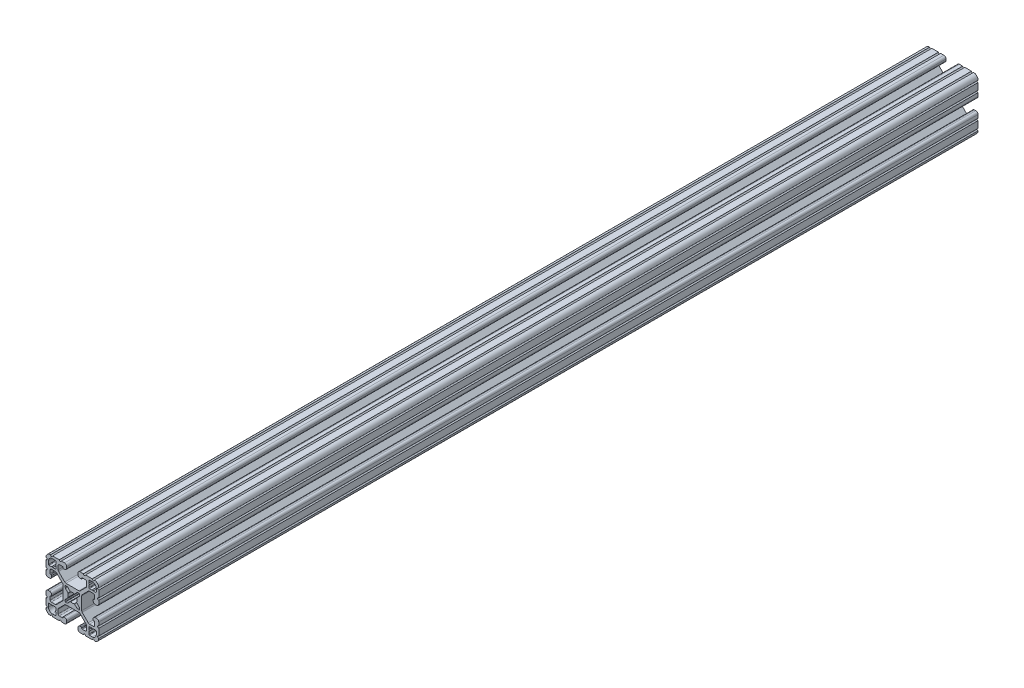
SolidWorks part; units mm, degrees
ref_plane "Front Plane" through (0, 0, 0) normal (0, 0, 1) x (1, 0, 0)
ref_plane "Top Plane" through (0, 0, 0) normal (0, 1, 0) x (1, 0, 0)
ref_plane "Right Plane" through (0, 0, 0) normal (1, 0, 0) x (0, 0, -1)
sketch "Sketch1" plane through (0, 0, 0) normal (0, 0, 1) x (1, 0, 0)
  line L0 (1.5823, 3.1988) -> (3.2921, 4.9085)
  line L1 (3.9207, 5.1689) -> (4.9149, 5.1689)
  line L2 (5.1689, 4.9149) -> (5.1689, 3.9207)
  line L3 (4.9085, 3.2921) -> (3.1988, 1.5823)
  line L4 (3.1988, -1.5823) -> (4.9085, -3.2921)
  line L5 (5.1689, -3.9207) -> (5.1689, -4.9149)
  line L6 (4.9149, -5.1689) -> (3.9207, -5.1689)
  line L7 (3.2921, -4.9085) -> (1.5823, -3.1988)
  line L8 (-1.5823, -3.1988) -> (-3.2921, -4.9085)
  line L9 (-3.9207, -5.1689) -> (-4.9149, -5.1689)
  line L10 (-5.1689, -4.9149) -> (-5.1689, -3.9207)
  line L11 (-4.9085, -3.2921) -> (-3.1988, -1.5823)
  line L12 (-3.1988, 1.5823) -> (-4.9085, 3.2921)
  line L13 (-5.1689, 3.9207) -> (-5.1689, 4.9149)
  line L14 (-4.9149, 5.1689) -> (-3.9207, 5.1689)
  line L15 (-3.2921, 4.9085) -> (-1.5823, 3.1988)
  line L16 (-11.8669, 14.0194) -> (-11.8669, 12.2479)
  line L17 (-12.2479, 11.8669) -> (-14.0195, 11.8669)
  line L18 (-14.0213, 11.8676) -> (-14.5575, 12.4039)
  line L19 (-14.5611, 12.4039) -> (-15.0973, 11.8676)
  line L20 (-15.0991, 11.8669) -> (-16.8707, 11.8669)
  line L21 (-17.2517, 12.2479) -> (-17.2517, 14.4577)
  line L22 (-14.4577, 17.2517) -> (-12.2479, 17.2517)
  line L23 (-11.8669, 16.8707) -> (-11.8669, 15.0991)
  line L24 (-11.8676, 15.0973) -> (-12.4039, 14.5611)
  line L25 (-12.4039, 14.5575) -> (-11.8676, 14.0212)
  line L26 (-14.0194, -11.8669) -> (-12.2479, -11.8669)
  line L27 (-11.8669, -12.2479) -> (-11.8669, -14.0195)
  line L28 (-11.8676, -14.0213) -> (-12.4039, -14.5575)
  line L29 (-12.4039, -14.5611) -> (-11.8676, -15.0973)
  line L30 (-11.8669, -15.0991) -> (-11.8669, -16.8707)
  line L31 (-12.2479, -17.2517) -> (-14.4577, -17.2517)
  line L32 (-17.2517, -14.4577) -> (-17.2517, -12.2479)
  line L33 (-16.8707, -11.8669) -> (-15.0991, -11.8669)
  line L34 (-15.0973, -11.8676) -> (-14.5611, -12.4039)
  line L35 (-14.5575, -12.4039) -> (-14.0212, -11.8676)
  line L36 (11.8669, -14.0194) -> (11.8669, -12.2479)
  line L37 (12.2479, -11.8669) -> (14.0195, -11.8669)
  line L38 (14.0213, -11.8676) -> (14.5575, -12.4039)
  line L39 (14.5611, -12.4039) -> (15.0973, -11.8676)
  line L40 (15.0991, -11.8669) -> (16.8707, -11.8669)
  line L41 (17.2517, -12.2479) -> (17.2517, -14.4577)
  line L42 (14.4577, -17.2517) -> (12.2479, -17.2517)
  line L43 (11.8669, -16.8707) -> (11.8669, -15.0991)
  line L44 (11.8676, -15.0973) -> (12.4039, -14.5611)
  line L45 (12.4039, -14.5575) -> (11.8676, -14.0212)
  line L46 (14.0194, 11.8669) -> (12.2479, 11.8669)
  line L47 (11.8669, 12.2479) -> (11.8669, 14.0195)
  line L48 (11.8676, 14.0213) -> (12.4039, 14.5575)
  line L49 (12.4039, 14.5611) -> (11.8676, 15.0973)
  line L50 (11.8669, 15.0991) -> (11.8669, 16.8707)
  line L51 (12.2479, 17.2517) -> (14.4577, 17.2517)
  line L52 (17.2517, 14.4577) -> (17.2517, 12.2479)
  line L53 (16.8707, 11.8669) -> (15.0991, 11.8669)
  line L54 (15.0973, 11.8676) -> (14.5611, 12.4039)
  line L55 (14.5575, 12.4039) -> (14.0212, 11.8676)
  line L56 (6.3498, -14.9848) -> (5.6531, -14.9848)
  line L57 (4.0778, -16.5601) -> (4.0778, -17.4747)
  line L58 (5.6531, -19.05) -> (7.9756, -19.05)
  line L59 (9.4996, -19.05) -> (14.2981, -19.05)
  line L60 (19.05, -14.3256) -> (19.05, -9.4996)
  line L61 (19.05, -7.9756) -> (19.05, -5.6531)
  line L62 (17.4747, -4.0778) -> (16.5601, -4.0778)
  line L63 (14.9848, -5.6531) -> (14.9848, -6.3498)
  line L64 (15.3661, -6.731) -> (15.6969, -6.731)
  line L65 (16.0782, -7.1122) -> (16.0782, -9.3968)
  line L66 (15.1881, -10.287) -> (12.3526, -10.2871)
  line L67 (11.4535, -9.9142) -> (7.1147, -5.5659)
  line L68 (6.7437, -4.6689) -> (6.7437, 4.6414)
  line L69 (7.1147, 5.5384) -> (11.481, 9.9142)
  line L70 (12.38, 10.2871) -> (15.1881, 10.287)
  line L71 (16.0782, 9.3968) -> (16.0782, 7.1122)
  line L72 (15.6969, 6.731) -> (15.3661, 6.731)
  line L73 (14.9848, 6.3498) -> (14.9848, 5.6531)
  line L74 (16.5601, 4.0778) -> (17.4747, 4.0778)
  line L75 (19.05, 5.6531) -> (19.05, 7.9756)
  line L76 (19.05, 9.4996) -> (19.05, 14.2981)
  line L77 (14.3256, 19.05) -> (9.4996, 19.05)
  line L78 (7.9756, 19.05) -> (5.6531, 19.05)
  line L79 (4.0778, 17.4747) -> (4.0778, 16.5601)
  line L80 (5.6531, 14.9848) -> (6.3498, 14.9848)
  line L81 (6.731, 15.3661) -> (6.731, 15.6969)
  line L82 (7.1122, 16.0782) -> (9.3968, 16.0782)
  line L83 (10.287, 15.1881) -> (10.2871, 12.3526)
  line L84 (9.9142, 11.4535) -> (5.5659, 7.1147)
  line L85 (4.6689, 6.7437) -> (-4.6414, 6.7437)
  line L86 (-5.5384, 7.1147) -> (-9.9142, 11.481)
  line L87 (-10.2871, 12.38) -> (-10.287, 15.1881)
  line L88 (-9.3968, 16.0782) -> (-7.1122, 16.0782)
  line L89 (-6.731, 15.6969) -> (-6.731, 15.3661)
  line L90 (-6.3498, 14.9848) -> (-5.6531, 14.9848)
  line L91 (-4.0778, 16.5601) -> (-4.0778, 17.4747)
  line L92 (-5.6531, 19.05) -> (-7.9756, 19.05)
  line L93 (-9.4996, 19.05) -> (-14.2981, 19.05)
  line L94 (-19.05, 14.3256) -> (-19.05, 9.4996)
  line L95 (-19.05, 7.9756) -> (-19.05, 5.6531)
  line L96 (-17.4747, 4.0778) -> (-16.5601, 4.0778)
  line L97 (-14.9848, 5.6531) -> (-14.9848, 6.3498)
  line L98 (-15.3661, 6.731) -> (-15.6969, 6.731)
  line L99 (-16.0782, 7.1122) -> (-16.0782, 9.3968)
  line L100 (-15.1881, 10.287) -> (-12.3526, 10.2871)
  line L101 (-11.4535, 9.9142) -> (-7.1147, 5.5659)
  line L102 (-6.7437, 4.6689) -> (-6.7437, -4.6414)
  line L103 (-7.1147, -5.5384) -> (-11.481, -9.9142)
  line L104 (-12.38, -10.2871) -> (-15.1881, -10.287)
  line L105 (-16.0782, -9.3968) -> (-16.0782, -7.1122)
  line L106 (-15.6969, -6.731) -> (-15.3661, -6.731)
  line L107 (-14.9848, -6.3498) -> (-14.9848, -5.6531)
  line L108 (-16.5601, -4.0778) -> (-17.4747, -4.0778)
  line L109 (-19.05, -5.6531) -> (-19.05, -7.9756)
  line L110 (-19.05, -9.4996) -> (-19.05, -14.2981)
  line L111 (-14.3256, -19.05) -> (-9.4996, -19.05)
  line L112 (-7.9756, -19.05) -> (-5.6531, -19.05)
  line L113 (-4.0778, -17.4747) -> (-4.0778, -16.5601)
  line L114 (-5.6531, -14.9848) -> (-6.3498, -14.9848)
  line L115 (-6.731, -15.3661) -> (-6.731, -15.6969)
  line L116 (-7.1122, -16.0782) -> (-9.3968, -16.0782)
  line L117 (-10.287, -15.1881) -> (-10.2871, -12.3526)
  line L118 (-9.9142, -11.4535) -> (-5.5659, -7.1147)
  line L119 (-4.6689, -6.7437) -> (4.6414, -6.7437)
  line L120 (5.5384, -7.1147) -> (9.9142, -11.481)
  line L121 (10.2871, -12.38) -> (10.287, -15.1881)
  line L122 (9.3968, -16.0782) -> (7.1122, -16.0782)
  line L123 (6.731, -15.6969) -> (6.731, -15.3661)
  arc A0 (1.178, 3.1119) -> (1.5823, 3.1988) centre (1.3129, 3.4682) ccw
  arc A1 (3.9207, 5.1689) -> (3.2921, 4.9085) centre (3.9207, 4.2799) ccw
  arc A2 (5.1689, 4.9149) -> (4.9149, 5.1689) centre (4.9149, 4.9149) ccw
  arc A3 (4.9085, 3.2921) -> (5.1689, 3.9207) centre (4.2799, 3.9207) ccw
  arc A4 (3.1988, 1.5823) -> (3.1119, 1.178) centre (3.4682, 1.3129) ccw
  arc A5 (3.1119, -1.178) -> (3.1119, 1.178) centre (0, 0) ccw
  arc A6 (3.1119, -1.178) -> (3.1988, -1.5823) centre (3.4682, -1.3129) ccw
  arc A7 (5.1689, -3.9207) -> (4.9085, -3.2921) centre (4.2799, -3.9207) ccw
  arc A8 (4.9149, -5.1689) -> (5.1689, -4.9149) centre (4.9149, -4.9149) ccw
  arc A9 (3.2921, -4.9085) -> (3.9207, -5.1689) centre (3.9207, -4.2799) ccw
  arc A10 (1.5823, -3.1988) -> (1.178, -3.1119) centre (1.3129, -3.4682) ccw
  arc A11 (-1.178, -3.1119) -> (1.178, -3.1119) centre (0, 0) ccw
  arc A12 (-1.178, -3.1119) -> (-1.5823, -3.1988) centre (-1.3129, -3.4682) ccw
  arc A13 (-3.9207, -5.1689) -> (-3.2921, -4.9085) centre (-3.9207, -4.2799) ccw
  arc A14 (-5.1689, -4.9149) -> (-4.9149, -5.1689) centre (-4.9149, -4.9149) ccw
  arc A15 (-4.9085, -3.2921) -> (-5.1689, -3.9207) centre (-4.2799, -3.9207) ccw
  arc A16 (-3.1988, -1.5823) -> (-3.1119, -1.178) centre (-3.4682, -1.3129) ccw
  arc A17 (-3.1119, 1.178) -> (-3.1119, -1.178) centre (0, 0) ccw
  arc A18 (-3.1119, 1.178) -> (-3.1988, 1.5823) centre (-3.4682, 1.3129) ccw
  arc A19 (-5.1689, 3.9207) -> (-4.9085, 3.2921) centre (-4.2799, 3.9207) ccw
  arc A20 (-4.9149, 5.1689) -> (-5.1689, 4.9149) centre (-4.9149, 4.9149) ccw
  arc A21 (-3.2921, 4.9085) -> (-3.9207, 5.1689) centre (-3.9207, 4.2799) ccw
  arc A22 (-1.5823, 3.1988) -> (-1.178, 3.1119) centre (-1.3129, 3.4682) ccw
  arc A23 (1.178, 3.1119) -> (-1.178, 3.1119) centre (0, 0) ccw
  arc A24 (-11.8669, 14.0194) -> (-11.8676, 14.0212) centre (-11.8694, 14.0194) ccw
  arc A25 (-12.2479, 11.8669) -> (-11.8669, 12.2479) centre (-12.2479, 12.2479) ccw
  arc A26 (-14.0213, 11.8676) -> (-14.0195, 11.8669) centre (-14.0195, 11.8694) ccw
  arc A27 (-14.5575, 12.4039) -> (-14.5611, 12.4039) centre (-14.5593, 12.4021) ccw
  arc A28 (-15.0991, 11.8669) -> (-15.0973, 11.8676) centre (-15.0991, 11.8694) ccw
  arc A29 (-17.2517, 12.2479) -> (-16.8707, 11.8669) centre (-16.8707, 12.2479) ccw
  arc A30 (-14.4577, 17.2517) -> (-17.2517, 14.4577) centre (-14.4577, 14.4577) ccw
  arc A31 (-11.8669, 16.8707) -> (-12.2479, 17.2517) centre (-12.2479, 16.8707) ccw
  arc A32 (-11.8676, 15.0973) -> (-11.8669, 15.0991) centre (-11.8694, 15.0991) ccw
  arc A33 (-12.4039, 14.5611) -> (-12.4039, 14.5575) centre (-12.4021, 14.5593) ccw
  arc A34 (-14.0194, -11.8669) -> (-14.0212, -11.8676) centre (-14.0194, -11.8694) ccw
  arc A35 (-11.8669, -12.2479) -> (-12.2479, -11.8669) centre (-12.2479, -12.2479) ccw
  arc A36 (-11.8676, -14.0213) -> (-11.8669, -14.0195) centre (-11.8694, -14.0195) ccw
  arc A37 (-12.4039, -14.5575) -> (-12.4039, -14.5611) centre (-12.4021, -14.5593) ccw
  arc A38 (-11.8669, -15.0991) -> (-11.8676, -15.0973) centre (-11.8694, -15.0991) ccw
  arc A39 (-12.2479, -17.2517) -> (-11.8669, -16.8707) centre (-12.2479, -16.8707) ccw
  arc A40 (-17.2517, -14.4577) -> (-14.4577, -17.2517) centre (-14.4577, -14.4577) ccw
  arc A41 (-16.8707, -11.8669) -> (-17.2517, -12.2479) centre (-16.8707, -12.2479) ccw
  arc A42 (-15.0973, -11.8676) -> (-15.0991, -11.8669) centre (-15.0991, -11.8694) ccw
  arc A43 (-14.5611, -12.4039) -> (-14.5575, -12.4039) centre (-14.5593, -12.4021) ccw
  arc A44 (11.8669, -14.0194) -> (11.8676, -14.0212) centre (11.8694, -14.0194) ccw
  arc A45 (12.2479, -11.8669) -> (11.8669, -12.2479) centre (12.2479, -12.2479) ccw
  arc A46 (14.0213, -11.8676) -> (14.0195, -11.8669) centre (14.0195, -11.8694) ccw
  arc A47 (14.5575, -12.4039) -> (14.5611, -12.4039) centre (14.5593, -12.4021) ccw
  arc A48 (15.0991, -11.8669) -> (15.0973, -11.8676) centre (15.0991, -11.8694) ccw
  arc A49 (17.2517, -12.2479) -> (16.8707, -11.8669) centre (16.8707, -12.2479) ccw
  arc A50 (14.4577, -17.2517) -> (17.2517, -14.4577) centre (14.4577, -14.4577) ccw
  arc A51 (11.8669, -16.8707) -> (12.2479, -17.2517) centre (12.2479, -16.8707) ccw
  arc A52 (11.8676, -15.0973) -> (11.8669, -15.0991) centre (11.8694, -15.0991) ccw
  arc A53 (12.4039, -14.5611) -> (12.4039, -14.5575) centre (12.4021, -14.5593) ccw
  arc A54 (14.0194, 11.8669) -> (14.0212, 11.8676) centre (14.0194, 11.8694) ccw
  arc A55 (11.8669, 12.2479) -> (12.2479, 11.8669) centre (12.2479, 12.2479) ccw
  arc A56 (11.8676, 14.0213) -> (11.8669, 14.0195) centre (11.8694, 14.0195) ccw
  arc A57 (12.4039, 14.5575) -> (12.4039, 14.5611) centre (12.4021, 14.5593) ccw
  arc A58 (11.8669, 15.0991) -> (11.8676, 15.0973) centre (11.8694, 15.0991) ccw
  arc A59 (12.2479, 17.2517) -> (11.8669, 16.8707) centre (12.2479, 16.8707) ccw
  arc A60 (17.2517, 14.4577) -> (14.4577, 17.2517) centre (14.4577, 14.4577) ccw
  arc A61 (16.8707, 11.8669) -> (17.2517, 12.2479) centre (16.8707, 12.2479) ccw
  arc A62 (15.0973, 11.8676) -> (15.0991, 11.8669) centre (15.0991, 11.8694) ccw
  arc A63 (14.5611, 12.4039) -> (14.5575, 12.4039) centre (14.5593, 12.4021) ccw
  arc A64 (6.731, -15.3661) -> (6.3498, -14.9848) centre (6.35, -15.3658) ccw
  arc A65 (5.6531, -14.9848) -> (4.0778, -16.5601) centre (5.6526, -16.5596) ccw
  arc A66 (4.0778, -17.4747) -> (5.6531, -19.05) centre (5.6526, -17.4752) ccw
  arc A67 (9.4996, -19.05) -> (7.9756, -19.05) centre (8.7376, -19.05) ccw
  arc A68 (15.8221, -19.0496) -> (14.2981, -19.05) centre (15.0601, -19.05) ccw
  arc A69 (15.8221, -19.0496) -> (19.0499, -15.8496) centre (15.875, -15.875) ccw
  arc A70 (19.05, -14.3256) -> (19.0499, -15.8496) centre (19.05, -15.0876) ccw
  arc A71 (19.05, -7.9756) -> (19.05, -9.4996) centre (19.05, -8.7376) ccw
  arc A72 (19.05, -5.6531) -> (17.4747, -4.0778) centre (17.4752, -5.6526) ccw
  arc A73 (16.5601, -4.0778) -> (14.9848, -5.6531) centre (16.5596, -5.6526) ccw
  arc A74 (14.9848, -6.3498) -> (15.3661, -6.731) centre (15.3658, -6.35) ccw
  arc A75 (16.0782, -7.1122) -> (15.6969, -6.731) centre (15.6972, -7.112) ccw
  arc A76 (15.1881, -10.287) -> (16.0782, -9.3968) centre (15.1892, -9.398) ccw
  arc A77 (11.4535, -9.9142) -> (12.3526, -10.2871) centre (12.3525, -9.0171) ccw
  arc A78 (6.7437, -4.6689) -> (7.1147, -5.5659) centre (8.0137, -4.6689) ccw
  arc A79 (7.1147, 5.5384) -> (6.7437, 4.6414) centre (8.0137, 4.6414) ccw
  arc A80 (12.38, 10.2871) -> (11.481, 9.9142) centre (12.38, 9.0171) ccw
  arc A81 (16.0782, 9.3968) -> (15.1881, 10.287) centre (15.1892, 9.398) ccw
  arc A82 (15.6969, 6.731) -> (16.0782, 7.1122) centre (15.6972, 7.112) ccw
  arc A83 (15.3661, 6.731) -> (14.9848, 6.3498) centre (15.3658, 6.35) ccw
  arc A84 (14.9848, 5.6531) -> (16.5601, 4.0778) centre (16.5596, 5.6526) ccw
  arc A85 (17.4747, 4.0778) -> (19.05, 5.6531) centre (17.4752, 5.6526) ccw
  arc A86 (19.05, 9.4996) -> (19.05, 7.9756) centre (19.05, 8.7376) ccw
  arc A87 (19.0496, 15.8221) -> (19.05, 14.2981) centre (19.05, 15.0601) ccw
  arc A88 (19.0496, 15.8221) -> (15.8496, 19.0499) centre (15.875, 15.875) ccw
  arc A89 (14.3256, 19.05) -> (15.8496, 19.0499) centre (15.0876, 19.05) ccw
  arc A90 (7.9756, 19.05) -> (9.4996, 19.05) centre (8.7376, 19.05) ccw
  arc A91 (5.6531, 19.05) -> (4.0778, 17.4747) centre (5.6526, 17.4752) ccw
  arc A92 (4.0778, 16.5601) -> (5.6531, 14.9848) centre (5.6526, 16.5596) ccw
  arc A93 (6.3498, 14.9848) -> (6.731, 15.3661) centre (6.35, 15.3658) ccw
  arc A94 (7.1122, 16.0782) -> (6.731, 15.6969) centre (7.112, 15.6972) ccw
  arc A95 (10.287, 15.1881) -> (9.3968, 16.0782) centre (9.398, 15.1892) ccw
  arc A96 (9.9142, 11.4535) -> (10.2871, 12.3526) centre (9.0171, 12.3525) ccw
  arc A97 (4.6689, 6.7437) -> (5.5659, 7.1147) centre (4.6689, 8.0137) ccw
  arc A98 (-5.5384, 7.1147) -> (-4.6414, 6.7437) centre (-4.6414, 8.0137) ccw
  arc A99 (-10.2871, 12.38) -> (-9.9142, 11.481) centre (-9.0171, 12.38) ccw
  arc A100 (-9.3968, 16.0782) -> (-10.287, 15.1881) centre (-9.398, 15.1892) ccw
  arc A101 (-6.731, 15.6969) -> (-7.1122, 16.0782) centre (-7.112, 15.6972) ccw
  arc A102 (-6.731, 15.3661) -> (-6.3498, 14.9848) centre (-6.35, 15.3658) ccw
  arc A103 (-5.6531, 14.9848) -> (-4.0778, 16.5601) centre (-5.6526, 16.5596) ccw
  arc A104 (-4.0778, 17.4747) -> (-5.6531, 19.05) centre (-5.6526, 17.4752) ccw
  arc A105 (-9.4996, 19.05) -> (-7.9756, 19.05) centre (-8.7376, 19.05) ccw
  arc A106 (-15.8221, 19.0496) -> (-14.2981, 19.05) centre (-15.0601, 19.05) ccw
  arc A107 (-15.8221, 19.0496) -> (-19.0499, 15.8496) centre (-15.875, 15.875) ccw
  arc A108 (-19.05, 14.3256) -> (-19.0499, 15.8496) centre (-19.05, 15.0876) ccw
  arc A109 (-19.05, 7.9756) -> (-19.05, 9.4996) centre (-19.05, 8.7376) ccw
  arc A110 (-19.05, 5.6531) -> (-17.4747, 4.0778) centre (-17.4752, 5.6526) ccw
  arc A111 (-16.5601, 4.0778) -> (-14.9848, 5.6531) centre (-16.5596, 5.6526) ccw
  arc A112 (-14.9848, 6.3498) -> (-15.3661, 6.731) centre (-15.3658, 6.35) ccw
  arc A113 (-16.0782, 7.1122) -> (-15.6969, 6.731) centre (-15.6972, 7.112) ccw
  arc A114 (-15.1881, 10.287) -> (-16.0782, 9.3968) centre (-15.1892, 9.398) ccw
  arc A115 (-11.4535, 9.9142) -> (-12.3526, 10.2871) centre (-12.3525, 9.0171) ccw
  arc A116 (-6.7437, 4.6689) -> (-7.1147, 5.5659) centre (-8.0137, 4.6689) ccw
  arc A117 (-7.1147, -5.5384) -> (-6.7437, -4.6414) centre (-8.0137, -4.6414) ccw
  arc A118 (-12.38, -10.2871) -> (-11.481, -9.9142) centre (-12.38, -9.0171) ccw
  arc A119 (-16.0782, -9.3968) -> (-15.1881, -10.287) centre (-15.1892, -9.398) ccw
  arc A120 (-15.6969, -6.731) -> (-16.0782, -7.1122) centre (-15.6972, -7.112) ccw
  arc A121 (-15.3661, -6.731) -> (-14.9848, -6.3498) centre (-15.3658, -6.35) ccw
  arc A122 (-14.9848, -5.6531) -> (-16.5601, -4.0778) centre (-16.5596, -5.6526) ccw
  arc A123 (-17.4747, -4.0778) -> (-19.05, -5.6531) centre (-17.4752, -5.6526) ccw
  arc A124 (-19.05, -9.4996) -> (-19.05, -7.9756) centre (-19.05, -8.7376) ccw
  arc A125 (-19.0496, -15.8221) -> (-19.05, -14.2981) centre (-19.05, -15.0601) ccw
  arc A126 (-19.0496, -15.8221) -> (-15.8496, -19.0499) centre (-15.875, -15.875) ccw
  arc A127 (-14.3256, -19.05) -> (-15.8496, -19.0499) centre (-15.0876, -19.05) ccw
  arc A128 (-7.9756, -19.05) -> (-9.4996, -19.05) centre (-8.7376, -19.05) ccw
  arc A129 (-5.6531, -19.05) -> (-4.0778, -17.4747) centre (-5.6526, -17.4752) ccw
  arc A130 (-4.0778, -16.5601) -> (-5.6531, -14.9848) centre (-5.6526, -16.5596) ccw
  arc A131 (-6.3498, -14.9848) -> (-6.731, -15.3661) centre (-6.35, -15.3658) ccw
  arc A132 (-7.1122, -16.0782) -> (-6.731, -15.6969) centre (-7.112, -15.6972) ccw
  arc A133 (-10.287, -15.1881) -> (-9.3968, -16.0782) centre (-9.398, -15.1892) ccw
  arc A134 (-9.9142, -11.4535) -> (-10.2871, -12.3526) centre (-9.0171, -12.3525) ccw
  arc A135 (-4.6689, -6.7437) -> (-5.5659, -7.1147) centre (-4.6689, -8.0137) ccw
  arc A136 (5.5384, -7.1147) -> (4.6414, -6.7437) centre (4.6414, -8.0137) ccw
  arc A137 (10.2871, -12.38) -> (9.9142, -11.481) centre (9.0171, -12.38) ccw
  arc A138 (9.3968, -16.0782) -> (10.287, -15.1881) centre (9.398, -15.1892) ccw
  arc A139 (6.731, -15.6969) -> (7.1122, -16.0782) centre (7.112, -15.6972) ccw
extrude "Extrude1" add sketch "Sketch1" against normal blind 635
